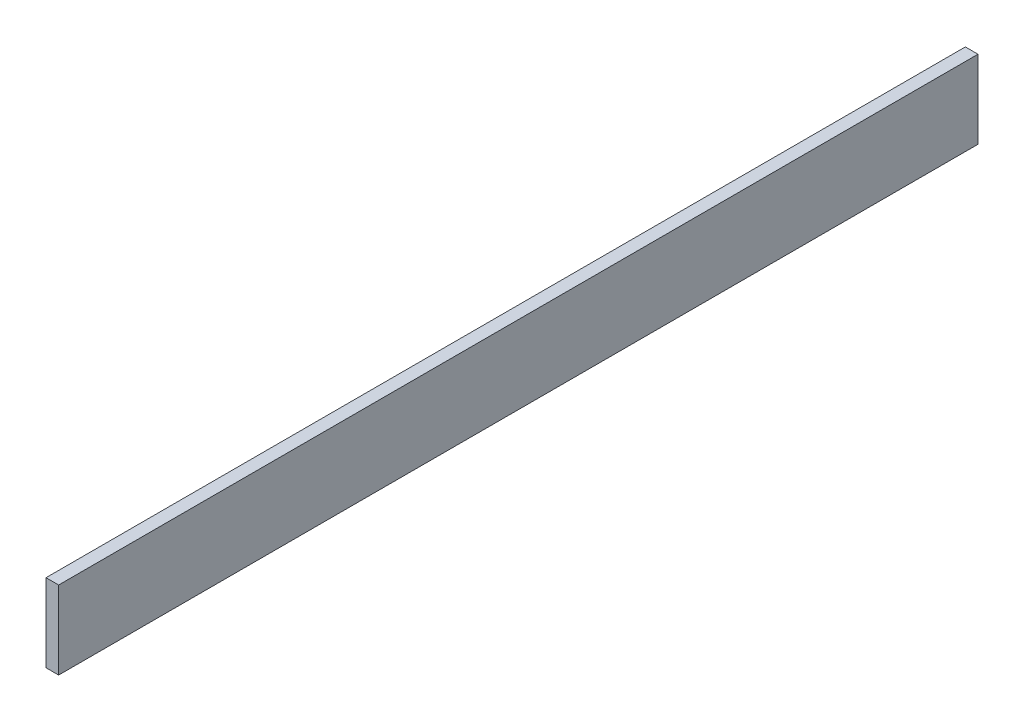
SolidWorks part; units mm, degrees
ref_plane "Front Plane" through (0, 0, 0) normal (0, 0, 1) x (1, 0, 0)
ref_plane "Top Plane" through (0, 0, 0) normal (0, 1, 0) x (1, 0, 0)
ref_plane "Right Plane" through (0, 0, 0) normal (1, 0, 0) x (0, 0, -1)
sketch "Sketch1" plane through (0, 0, 0) normal (1, 0, 0) x (0, 0, -1)
  line L1 (-416.0941, 114.4861) -> (2352.5059, 114.4861)
  line L2 (-416.0941, 114.4861) -> (-416.0941, 349.4361)
  line L3 (-416.0941, 349.4361) -> (2352.5059, 349.4361)
  line L4 (2352.5059, 114.4861) -> (2352.5059, 349.4361)
  dimension "D1" = 234.95
  dimension "D2" = 2768.6
extrude "Boss-Extrude1" add sketch "Sketch1" along normal blind 38.1
